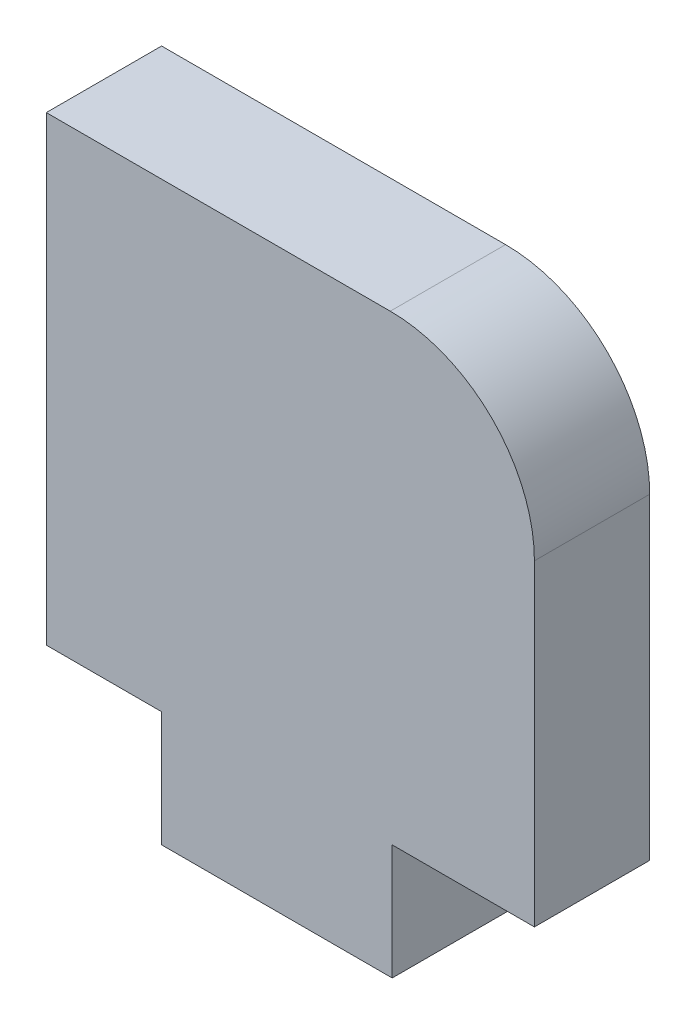
SolidWorks part; units mm, degrees
ref_plane "Front Plane" through (0, 0, 0) normal (0, 0, 1) x (1, 0, 0)
ref_plane "Top Plane" through (0, 0, 0) normal (0, 1, 0) x (1, 0, 0)
ref_plane "Right Plane" through (0, 0, 0) normal (1, 0, 0) x (0, 0, -1)
sketch "Sketch1" plane through (0, 0, 0) normal (0, 0, 1) x (1, 0, 0)
  line L0 (6.0757, -11) -> (11.0089, -11)
  line L1 (-1.9243, -11) -> (-5.9243, -11)
  line L2 (-5.9243, -11) -> (-5.9243, 5)
  line L3 (-5.9243, 5) -> (6.0089, 5)
  line L4 (6.0757, -11) -> (6.0757, -15)
  line L5 (6.0757, -15) -> (-1.9243, -15)
  line L6 (-1.9243, -15) -> (-1.9243, -11)
  line L7 (11.0089, 0) -> (11.0089, -11)
  arc A0 (11.0089, 0) -> (6.0089, 5) centre (6.0089, 0) ccw
  dimension "D1" = 5
  dimension "D2" = 6.0757
  dimension "D3" = 11.0089
  dimension "D4" = 1.9243
  dimension "D5" = 5.9243
  dimension "D6" = 11
extrude "Boss-Extrude1" add sketch "Sketch1" along normal blind 4
